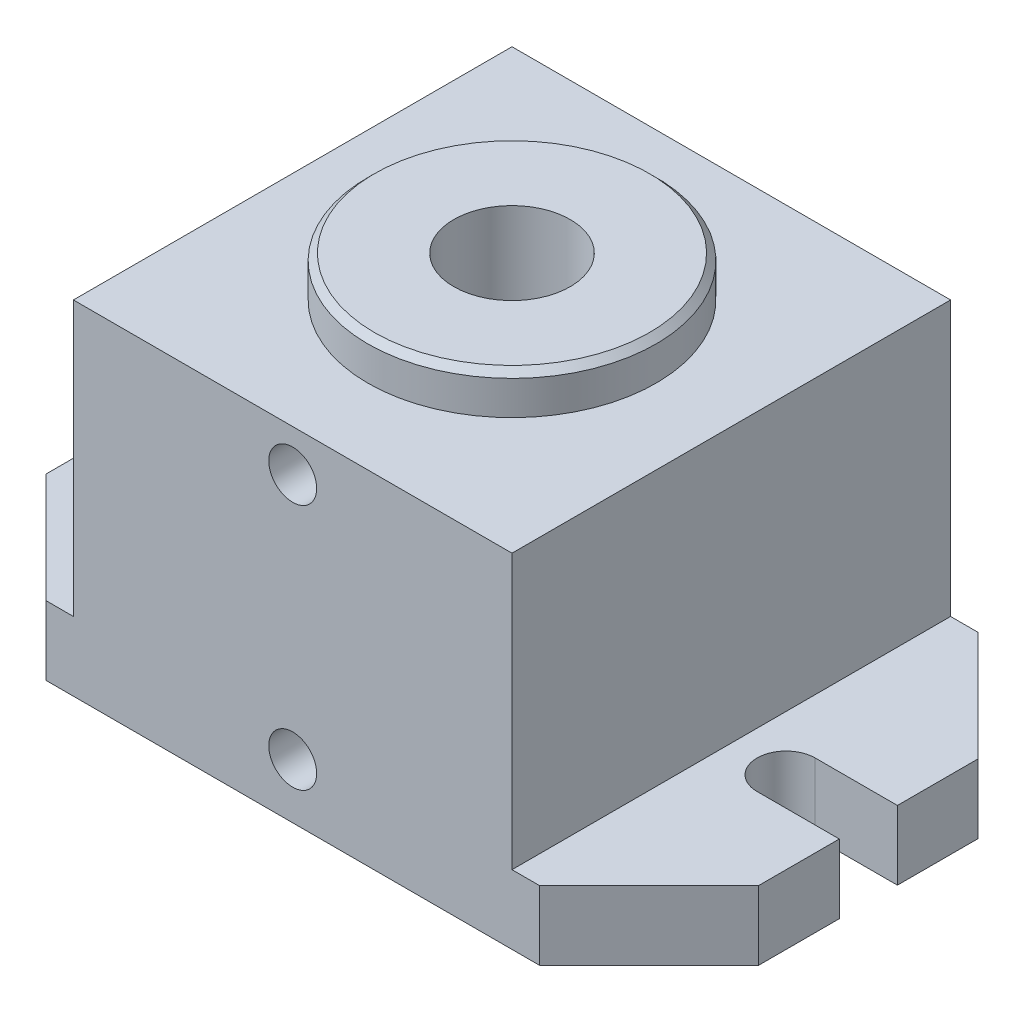
SolidWorks part; units mm, degrees
material "Alloy Steel"
ref_plane "Front Plane" through (0, 0, 0) normal (0, 0, 1) x (1, 0, 0)
ref_plane "Top Plane" through (0, 0, 0) normal (0, 1, 0) x (1, 0, 0)
ref_plane "Right Plane" through (0, 0, 0) normal (1, 0, 0) x (0, 0, -1)
sketch "Sketch1" plane through (0, 0, 0) normal (0, 1, 0) x (1, 0, 0)
  line L0 (-50.8, -50.8) -> (50.8, -50.8)
  line L1 (50.8, -50.8) -> (50.8, 50.8)
  line L2 (50.8, 50.8) -> (-50.8, 50.8)
  line L3 (-50.8, 50.8) -> (-50.8, -50.8)
  line L4 (-55.88, 0) -> (55.88, 0) construction
  line L5 (0, 0.7573) -> (0, -54.4639) construction
  dimension "D1" = 101.6
  dimension "D2" = 50.8
  dimension "D3" = 101.6
extrude "Extrude1" add sketch "Sketch1" along normal blind 79.502
sketch "Sketch2" plane through (0, 79.502, 0) normal (0, 1, 0) x (-1, 0, 0)
  circle A0 centre (0, 0) radius 33.401
  dimension "D1" = 66.802
extrude "Extrude2" add sketch "Sketch2" along normal blind 9.398
chamfer "Chamfer1" distance 1.524 angle 45 1 edges at (0, 88.9, 33.401)
sketch "Sketch3" plane through (0, 88.9, 0) normal (0, 1, 0) x (1, 0, 0)
  circle A0 centre (0, 0) radius 13.4874
  dimension "D1" = 26.9748
extrude "Cut-Extrude1" cut sketch "Sketch3" against normal through all
sketch "Sketch7" plane through (0, 0, 0) normal (0, -1, 0) x (1, 0, 0)
  line L0 (0, 0) -> (0, -68.8657) construction
  line L1 (50.8, 50.8) -> (82.55, 50.8)
  line L2 (50.8, 50.8) -> (50.8, -50.8)
  line L3 (50.8, -50.8) -> (82.55, -50.8)
  line L4 (82.55, 50.8) -> (82.55, 6.731)
  line L5 (0, 0) -> (71.9698, 0) construction
  line L6 (50.8, -50.8) -> (-50.8, -50.8) construction
  line L7 (63.5, 6.731) -> (82.55, 6.731)
  line L8 (63.5, -6.731) -> (82.55, -6.731)
  line L9 (82.55, -6.731) -> (82.55, -50.8)
  line L10 (-82.55, -6.731) -> (-82.55, -50.8)
  line L11 (-63.5, -6.731) -> (-82.55, -6.731)
  line L12 (-63.5, 6.731) -> (-82.55, 6.731)
  line L13 (-82.55, 50.8) -> (-82.55, 6.731)
  line L14 (-50.8, -50.8) -> (-82.55, -50.8)
  line L15 (-50.8, 50.8) -> (-50.8, -50.8)
  line L16 (-50.8, 50.8) -> (-82.55, 50.8)
  arc A0 (63.5, 6.731) -> (63.5, -6.731) centre (63.5, 0) ccw
  arc A1 (-63.5, 6.731) -> (-63.5, -6.731) centre (-63.5, 0) cw
  dimension "D1" = 165.1
  dimension "D2" = 13.462
  dimension "D3" = 19.05
extrude "Extrude3" add sketch "Sketch7" against normal blind 16.002
chamfer "Chamfer2" distance 25.4 distance2 25.4 4 edges at (-82.55, 8.001, -50.8) (82.55, 8.001, -50.8) (82.55, 8.001, 50.8) (-82.55, 8.001, 50.8)
sketch "Sketch8" plane through (0, 0, 50.8) normal (0, 0, 1) x (1, 0, 0)
  circle A0 centre (0, 69.85) radius 5.5499
  circle A1 centre (0, 12.7) radius 5.5499
  dimension "D1" = 11.0998
  dimension "D2" = 57.15
  dimension "D3" = 12.7
extrude "Cut-Extrude3" cut sketch "Sketch8" against normal blind 12.7
